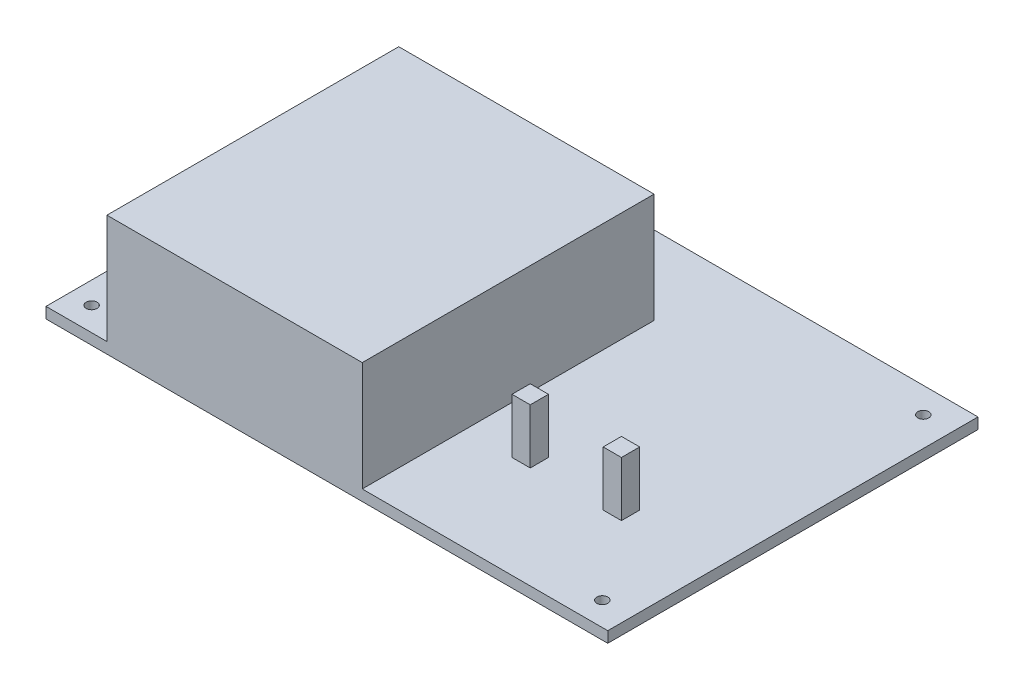
SolidWorks part; units mm, degrees
ref_plane "Front Plane" through (0, 0, 0) normal (0, 0, 1) x (1, 0, 0)
ref_plane "Top Plane" through (0, 0, 0) normal (0, 1, 0) x (1, 0, 0)
ref_plane "Right Plane" through (0, 0, 0) normal (1, 0, 0) x (0, 0, -1)
sketch "Esquisse1" plane through (0, 0, 0) normal (0, 1, 0) x (1, 0, 0)
  line L1 (-77, -50.75) -> (77, -50.75)
  line L2 (-77, -50.75) -> (-77, 50.75)
  line L3 (-77, 50.75) -> (77, 50.75)
  line L4 (77, -50.75) -> (77, 50.75)
  line L5 (-77, -50.75) -> (77, 50.75) construction
  line L6 (-77, 50.75) -> (77, -50.75) construction
  point P0 (0, 0)
  dimension "D1" = 101.5
  dimension "D2" = 154
extrude "Boss.-Extru.1" add sketch "Esquisse1" along normal blind 3
sketch "Esquisse2" plane through (0, 3, 0) normal (0, 1, 0) x (1, 0, 0)
  line L0 (-77, 50.75) -> (-77, -50.75) construction
  line L1 (77, 50.75) -> (-77, 50.75) construction
  circle A0 centre (-71, 43.75) radius 1.5
  circle A1 centre (69, 43.75) radius 1.5
  circle A2 centre (-71, -44.25) radius 1.5
  circle A3 centre (69, -44.25) radius 1.5
  dimension "D3" = 3
  dimension "D4" = 3
  dimension "D7" = 3
  dimension "D10" = 3
  dimension "D1" = 6
  dimension "D2" = 7
  dimension "D5" = 140
  dimension "D6" = 88
  dimension "D8" = 140
  dimension "D9" = 88
extrude "Enlèv. mat.-Extru.1" cut sketch "Esquisse2" against normal blind 3
sketch "Esquisse3" plane through (0, 3, 0) normal (0, 1, 0) x (1, 0, 0)
  line L0 (-77, 50.75) -> (-77, -50.75) construction
  line L1 (-60.3, -50.75) -> (9.7, -50.75)
  line L2 (-60.3, -50.75) -> (-60.3, 29.25)
  line L3 (-60.3, 29.25) -> (9.7, 29.25)
  line L4 (9.7, -50.75) -> (9.7, 29.25)
  line L5 (-60.3, -50.75) -> (9.7, 29.25) construction
  line L6 (-60.3, 29.25) -> (9.7, -50.75) construction
  line L7 (77, 50.75) -> (-77, 50.75) construction
  point P0 (-25.3, -10.75)
  dimension "D1" = 80
  dimension "D2" = 70
  dimension "D3" = 16.7
  dimension "D4" = 21.5
extrude "Boss.-Extru.2" add sketch "Esquisse3" along normal blind 30
sketch "Esquisse4" plane through (0, 3, 0) normal (0, 1, 0) x (1, 0, 0)
  line L0 (77, -50.75) -> (77, 50.75) construction
  line L1 (22.75, -22.75) -> (27.75, -22.75)
  line L2 (22.75, -22.75) -> (22.75, -17.75)
  line L3 (22.75, -17.75) -> (27.75, -17.75)
  line L4 (27.75, -22.75) -> (27.75, -17.75)
  line L5 (22.75, -22.75) -> (27.75, -17.75) construction
  line L6 (22.75, -17.75) -> (27.75, -22.75) construction
  line L7 (47.75, -22.75) -> (52.75, -22.75)
  line L8 (47.75, -22.75) -> (47.75, -17.75)
  line L9 (47.75, -17.75) -> (52.75, -17.75)
  line L10 (52.75, -22.75) -> (52.75, -17.75)
  line L11 (47.75, -22.75) -> (52.75, -17.75) construction
  line L12 (47.75, -17.75) -> (52.75, -22.75) construction
  line L13 (9.7, -50.75) -> (77, -50.75) construction
  point P0 (25.25, -20.25)
  point P5 (50.25, -20.25)
  dimension "D1" = 5
  dimension "D2" = 5
  dimension "D3" = 5
  dimension "D4" = 5
  dimension "D5" = 30
  dimension "D6" = 24.25
  dimension "D7" = 28
  dimension "D8" = 28
extrude "Boss.-Extru.3" add sketch "Esquisse4" along normal blind 15
sketch "Esquisse5" plane through (0, 0, 0) normal (0, -1, 0) x (1, 0, 0)
  line L0 (77, 0) -> (-77, 0) construction
  line L1 (77, 50.75) -> (77, -50.75) construction
  line L2 (-77, -50.75) -> (-77, 50.75) construction
  circle A0 centre (0, 0) radius 5
  dimension "D1" = 10
extrude "Enlèv. mat.-Extru.2" cut sketch "Esquisse5" against normal blind 1
